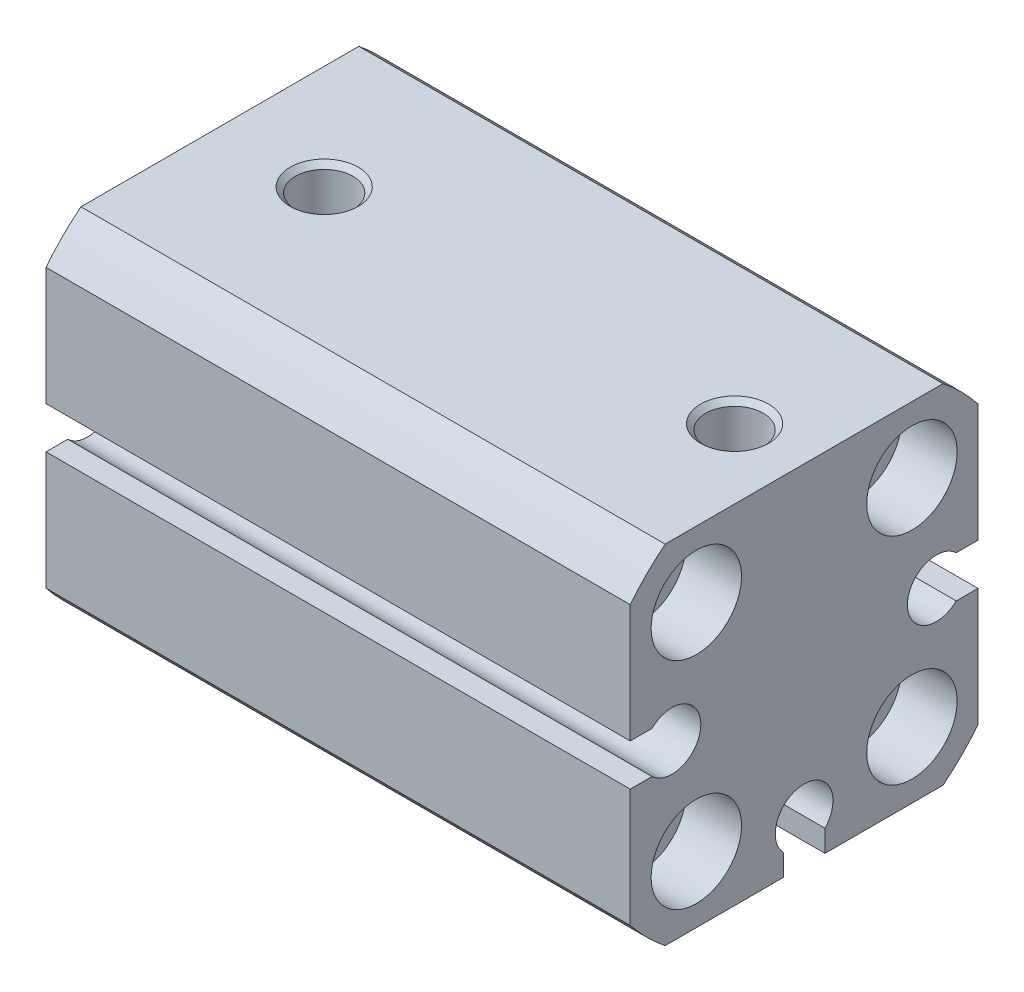
SolidWorks part; units mm, degrees
ref_plane "Front Plane" through (0, 0, 0) normal (0, 0, 1) x (1, 0, 0)
ref_plane "Top Plane" through (0, 0, 0) normal (0, 1, 0) x (1, 0, 0)
ref_plane "Right Plane" through (0, 0, 0) normal (1, 0, 0) x (0, 0, -1)
ref_plane "Plane1" through (42, 0, 0) normal (1, 0, 0) x (0, 0, -1)
sketch "Sketch1" plane through (42, 0, 0) normal (1, 0, 0) x (0, 0, -1)
  line L0 (-12.5, 9.9875) -> (-12.5, -9.9875)
  line L1 (-9.9875, -12.5) -> (9.9875, -12.5)
  line L2 (12.5, -9.9875) -> (12.5, 9.9875)
  line L3 (9.9875, 12.5) -> (-9.9875, 12.5)
  arc A0 (-12.5, -9.9875) -> (-9.9875, -12.5) centre (0, 0) ccw
  arc A1 (9.9875, -12.5) -> (12.5, -9.9875) centre (0, 0) ccw
  arc A2 (12.5, 9.9875) -> (9.9875, 12.5) centre (0, 0) ccw
  arc A3 (-9.9875, 12.5) -> (-12.5, 9.9875) centre (0, 0) ccw
extrude "Boss-Extrude1" add sketch "Sketch1" against normal blind 42
sketch "Sketch2" plane through (0, 0, 0) normal (-1, 0, 0) x (0, 0, 1)
  line L0 (12.5, -1.5) -> (12.5, 1.5)
  line L1 (12.5, 1.5) -> (10.9337, 1.5)
  line L2 (10.9337, -1.5) -> (12.5, -1.5)
  arc A0 (10.9337, 1.5) -> (10.9337, -1.5) centre (9.5, 0) cw
extrude "Cut-Extrude1" cut sketch "Sketch2" against normal through all
sketch "Sketch3" plane through (0, 0, 0) normal (-1, 0, 0) x (0, 0, 1)
  line L0 (-1.5, -12.5) -> (1.5, -12.5)
  line L1 (1.5, -12.5) -> (1.5, -10.9337)
  line L2 (-1.5, -10.9337) -> (-1.5, -12.5)
  arc A0 (1.5, -10.9337) -> (-1.5, -10.9337) centre (0, -9.5) cw
extrude "Cut-Extrude2" cut sketch "Sketch3" against normal through all
sketch "Sketch4" plane through (0, 0, 0) normal (-1, 0, 0) x (0, 0, 1)
  line L0 (-12.5, 1.5) -> (-12.5, -1.5)
  line L1 (-12.5, -1.5) -> (-10.9337, -1.5)
  line L2 (-10.9337, 1.5) -> (-12.5, 1.5)
  arc A0 (-10.9337, -1.5) -> (-10.9337, 1.5) centre (-9.5, 0) cw
extrude "Cut-Extrude3" cut sketch "Sketch4" against normal through all
sketch "Sketch5" plane through (0, 0, 0) normal (0, 0, 1) x (1, 0, 0)
  line L0 (0, 6.5) -> (0, 0)
  line L1 (0, 0) -> (36, 0)
  line L2 (36, 0) -> (36, 6)
  line L3 (36, 6) -> (11, 6)
  line L4 (11, 6) -> (11, 3)
  line L5 (11, 3) -> (1.2, 3)
  line L6 (1.2, 3) -> (1.2, 6.5)
  line L7 (1.2, 6.5) -> (0, 6.5)
  line L8 (0, 0) -> (36, 0) construction
revolve "Cut-Revolve1" cut sketch "Sketch5" angle 360 about L8
ref_plane "Plane2" through (0, 0, -7.75) normal (0, 0, -1) x (-1, 0, 0)
sketch "Sketch6" plane through (0, 0, -7.75) normal (0, 0, -1) x (-1, 0, 0)
  line L0 (-42, 11) -> (-42, 7.75)
  line L1 (-42, 7.75) -> (0, 7.75)
  line L2 (0, 7.75) -> (0, 11)
  line L3 (0, 11) -> (-4, 11)
  line L4 (-4, 11) -> (-4, 9.371)
  line L5 (-4, 9.371) -> (-11, 9.371)
  line L6 (-11, 9.371) -> (-11.0745, 9.5)
  line L7 (-11.0745, 9.5) -> (-30.9255, 9.5)
  line L8 (-30.9255, 9.5) -> (-31, 9.371)
  line L9 (-31, 9.371) -> (-38, 9.371)
  line L10 (-38, 9.371) -> (-38, 11)
  line L11 (-38, 11) -> (-42, 11)
  line L12 (-42, 7.75) -> (0, 7.75) construction
revolve "Cut-Revolve2" cut sketch "Sketch6" angle 360 about L12
sketch "Sketch7" plane through (0, 0, -7.75) normal (0, 0, -1) x (-1, 0, 0)
  line L0 (-42, -4.5) -> (-42, -7.75)
  line L1 (-42, -7.75) -> (0, -7.75)
  line L2 (0, -7.75) -> (0, -4.5)
  line L3 (0, -4.5) -> (-4, -4.5)
  line L4 (-4, -4.5) -> (-4, -6.129)
  line L5 (-4, -6.129) -> (-11, -6.129)
  line L6 (-11, -6.129) -> (-11.0745, -6)
  line L7 (-11.0745, -6) -> (-30.9255, -6)
  line L8 (-30.9255, -6) -> (-31, -6.129)
  line L9 (-31, -6.129) -> (-38, -6.129)
  line L10 (-38, -6.129) -> (-38, -4.5)
  line L11 (-38, -4.5) -> (-42, -4.5)
  line L12 (-42, -7.75) -> (0, -7.75) construction
revolve "Cut-Revolve3" cut sketch "Sketch7" angle 360 about L12
ref_plane "Plane3" through (0, 0, 7.75) normal (0, 0, -1) x (-1, 0, 0)
sketch "Sketch8" plane through (0, 0, 7.75) normal (0, 0, -1) x (-1, 0, 0)
  line L0 (-42, -4.5) -> (-42, -7.75)
  line L1 (-42, -7.75) -> (0, -7.75)
  line L2 (0, -7.75) -> (0, -4.5)
  line L3 (0, -4.5) -> (-4, -4.5)
  line L4 (-4, -4.5) -> (-4, -6.129)
  line L5 (-4, -6.129) -> (-11, -6.129)
  line L6 (-11, -6.129) -> (-11.0745, -6)
  line L7 (-11.0745, -6) -> (-30.9255, -6)
  line L8 (-30.9255, -6) -> (-31, -6.129)
  line L9 (-31, -6.129) -> (-38, -6.129)
  line L10 (-38, -6.129) -> (-38, -4.5)
  line L11 (-38, -4.5) -> (-42, -4.5)
  line L12 (-42, -7.75) -> (0, -7.75) construction
revolve "Cut-Revolve4" cut sketch "Sketch8" angle 360 about L12
sketch "Sketch9" plane through (0, 0, 7.75) normal (0, 0, -1) x (-1, 0, 0)
  line L0 (-42, 11) -> (-42, 7.75)
  line L1 (-42, 7.75) -> (0, 7.75)
  line L2 (0, 7.75) -> (0, 11)
  line L3 (0, 11) -> (-4, 11)
  line L4 (-4, 11) -> (-4, 9.371)
  line L5 (-4, 9.371) -> (-11, 9.371)
  line L6 (-11, 9.371) -> (-11.0745, 9.5)
  line L7 (-11.0745, 9.5) -> (-30.9255, 9.5)
  line L8 (-30.9255, 9.5) -> (-31, 9.371)
  line L9 (-31, 9.371) -> (-38, 9.371)
  line L10 (-38, 9.371) -> (-38, 11)
  line L11 (-38, 11) -> (-42, 11)
  line L12 (-42, 7.75) -> (0, 7.75) construction
revolve "Cut-Revolve5" cut sketch "Sketch9" angle 360 about L12
ref_plane "Plane4" through (0, 0, 9.5) normal (0, 0, 1) x (1, 0, 0)
sketch "Sketch10" plane through (0, 0, 9.5) normal (0, 0, 1) x (1, 0, 0)
  line L0 (0, 2.075) -> (0, 0)
  line L1 (0, 0) -> (42, 0)
  line L2 (42, 0) -> (42, 2.075)
  line L3 (42, 2.075) -> (0, 2.075)
  line L4 (0, 0) -> (42, 0) construction
revolve "Cut-Revolve6" cut sketch "Sketch10" angle 360 about L4
sketch "Sketch11" plane through (0, 0, 0) normal (0, 0, 1) x (1, 0, 0)
  line L0 (0, -7.425) -> (0, -9.5)
  line L1 (0, -9.5) -> (42, -9.5)
  line L2 (42, -9.5) -> (42, -7.425)
  line L3 (42, -7.425) -> (0, -7.425)
  line L4 (0, -9.5) -> (42, -9.5) construction
revolve "Cut-Revolve7" cut sketch "Sketch11" angle 360 about L4
ref_plane "Plane5" through (0, 0, -9.5) normal (0, 0, 1) x (1, 0, 0)
sketch "Sketch12" plane through (0, 0, -9.5) normal (0, 0, 1) x (1, 0, 0)
  line L0 (0, 2.075) -> (0, 0)
  line L1 (0, 0) -> (42, 0)
  line L2 (42, 0) -> (42, 2.075)
  line L3 (42, 2.075) -> (0, 2.075)
  line L4 (0, 0) -> (42, 0) construction
revolve "Cut-Revolve8" cut sketch "Sketch12" angle 360 about L4
hole_wizard "M3.5 Clearance Hole1" positions "Sketch14" profile "Sketch13" hole size "M3.5" standard "ANSI Metric"
sketch "Sketch14" plane through (0, 12.5, 0) normal (0, 1, 0) x (1, 0, 0)
  point P0 (7.5, 0)
  point P1 (37, 0)
sketch "Sketch13" plane through (7.5, 12.5, 0) normal (1, 0, 0) x (0, 0, 1)
  line L0 (0, 0) -> (0, 6.1934)
  line L1 (0, 6.1934) -> (2.067, 5)
  line L2 (2.067, 5) -> (2.067, 0)
  line L5 (2.067, 0) -> (0, 0)
  line L10 (0, 6.1934) -> (-2.067, 5) construction
  line L11 (0, -6.35) -> (0, 107.95) construction
  dimension "Hole Dia." = 4.134
  dimension "Hole Depth" = 5
  dimension "Drill Angle" = 120
chamfer "Chamfer1" distance 0.379 angle 45 10 edges at (38, 7.75, -6.129) (38, -7.75, -6.129) (37, 12.5, 2.067) (38, 7.75, 9.371) (4, 7.75, -6.129) (4, -7.75, 9.371) (7.5, 12.5, 2.067) (38, -7.75, 9.371) (4, 7.75, 9.371) (4, -7.75, -6.129)
